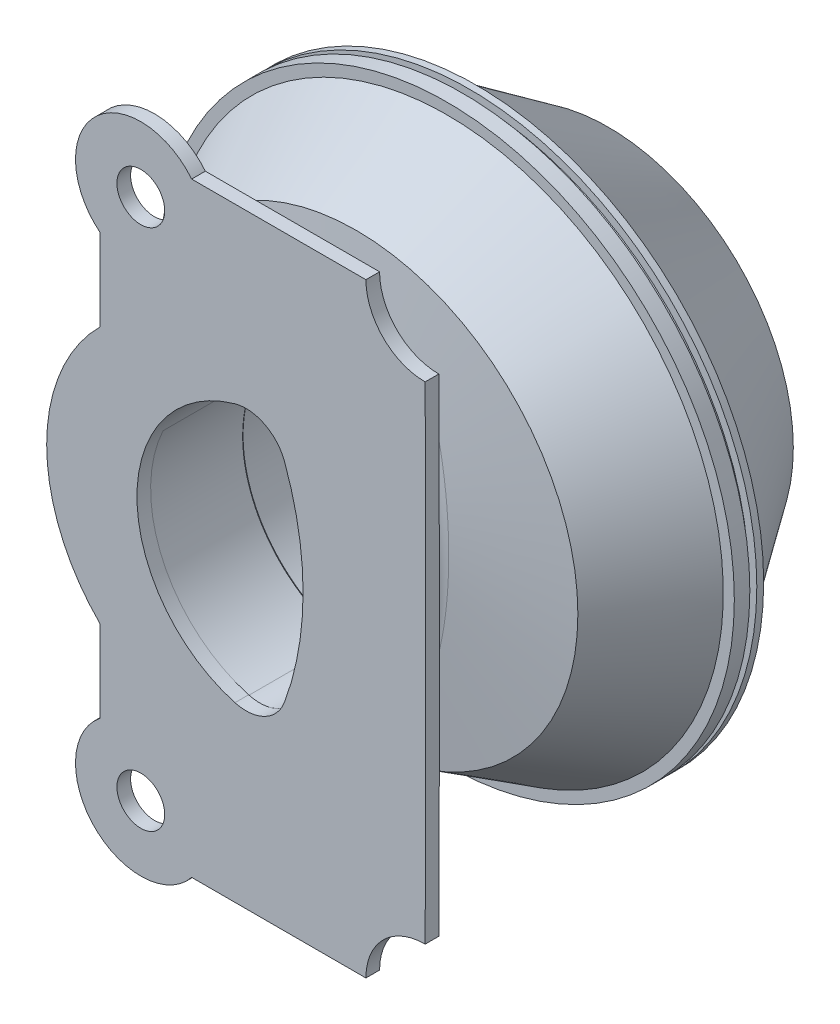
SolidWorks part; units mm, degrees
ref_plane "Front Plane" through (0, 0, 0) normal (0, 0, 1) x (1, 0, 0)
ref_plane "Top Plane" through (0, 0, 0) normal (0, 1, 0) x (1, 0, 0)
ref_plane "Right Plane" through (0, 0, 0) normal (1, 0, 0) x (0, 0, -1)
sketch "Sketch1" plane through (0, 0, 0) normal (0, 1, 0) x (1, 0, 0)
  line L0 (0, 0) -> (-41.1885, 4.2999)
  line L1 (-41.1885, 4.2999) -> (-51.3591, 21.1683)
  line L2 (-51.3591, 21.1683) -> (-53.4092, 21.1683)
  line L3 (-53.4092, 21.1683) -> (-53.4092, 24.0516)
  line L4 (-53.4092, 24.0516) -> (-51.9382, 24.0516)
  line L5 (-51.9382, 24.0516) -> (-51.9382, 25.3468)
  line L6 (-51.9382, 25.3468) -> (-53.4092, 25.3468)
  line L7 (-53.4092, 25.3468) -> (-53.4092, 26.625)
  line L8 (-53.4092, 26.625) -> (-51.4678, 26.625)
  line L9 (-51.4678, 26.625) -> (-34.3992, 51.1461)
  line L10 (-34.3992, 51.1461) -> (0, 57.3101)
  line L11 (0, 57.3101) -> (0, 0) construction
  line L12 (0, 0) -> (0, 57.3101)
  dimension "D1" = 57.4512
revolve "Revolve1" add sketch "Sketch1" angle 360 about L11
sketch "Sketch2" plane through (0, 0, 0) normal (0, 0, 1) x (1, 0, 0)
  arc A0 (-0.5749, 23.8806) -> (-0.5749, -24.2496) centre (6.2102, -0.1845) ccw
  arc A1 (8.6443, 19.1775) -> (8.6443, -19.5465) centre (-43.9843, -0.1845) cw
  arc A2 (8.6443, 19.1775) -> (-0.5749, 23.8806) centre (1.4929, 16.5465) ccw
  arc A3 (8.6443, -19.5465) -> (-0.5749, -24.2496) centre (1.4929, -16.9155) cw
  arc A4 (13.4119, 20.9315) -> (13.4119, -21.3005) centre (-43.9843, -0.1845) cw
  arc A5 (13.4119, -21.3005) -> (-1.9535, -29.139) centre (1.4929, -16.9155) cw
  arc A6 (-1.9535, 28.77) -> (-1.9535, -29.139) centre (6.2102, -0.1845) ccw
  arc A7 (13.4119, 20.9315) -> (-1.9535, 28.77) centre (1.4929, 16.5465) ccw
  dimension "D1" = 5.08
extrude "Extrude1" add sketch "Sketch2" along normal blind 15.24 and the other way up to next
fillet "Fillet1" radius 2.54 4 edges at (-23.8298, 1.4298, -2.4922) (6.4239, -28.6192, -3.0621) (17.1636, -1.2558, -1.7966) (6.4242, 28.2501, -3.0245)
ref_plane "Plane1" through (0, 0, 15.24) normal (0, 0, 1) x (1, 0, 0)
sketch "Sketch3" plane through (0, 0, 15.24) normal (0, 0, 1) x (1, 0, 0)
  line L0 (-25.6087, 23.8607) -> (-25.6087, 39.1449)
  line L1 (34.8116, -56.22) -> (-8.5336, -56.22)
  line L3 (34.8116, 56.22) -> (-8.5336, 56.22)
  line L4 (-25.6087, -39.1449) -> (-25.6087, -23.8607)
  arc A0 (34.8116, -56.22) -> (34.8116, 56.22) centre (-8901.9101, 0) ccw
  arc A1 (-25.6087, 23.8607) -> (-25.6087, -23.8607) centre (-1.748, 0) ccw
  arc A4 (-8.5336, 56.22) -> (-25.6087, 39.1449) centre (-17.9887, 48.6) ccw
  arc A5 (-25.6087, -39.1449) -> (-8.5336, -56.22) centre (-17.9887, -48.6) ccw
extrude "Extrude2" add sketch "Sketch3" along normal blind 2.54
sketch "Sketch4" plane through (173.7459, 16.0148, 17.78) normal (0, 0, 1) x (1, 0, 0)
  circle A0 centre (-191.7346, 32.5852) radius 4.445
  circle A1 centre (-191.7346, -64.6148) radius 4.445
  dimension "D1" = 8.89
extrude "Cut-Extrude1" cut sketch "Sketch4" against normal up to next
fillet "Fillet2" radius 2.54 4 edges at (17.173, -0.1845, 15.24) (7.2641, -28.2285, 15.24) (-23.8731, -0.1845, 15.24) (7.2641, 27.8595, 15.24)
sketch "Sketch5" plane through (0, 0, 17.78) normal (0, 0, 1) x (1, 0, 0)
  circle A0 centre (34.8116, 56.22) radius 10.9518
  circle A1 centre (34.8116, -56.22) radius 10.9518
extrude "Cut-Extrude2" cut sketch "Sketch5" against normal blind 2.54
sketch "Sketch6" plane through (25.8959, 34.9259, 17.78) normal (0, 0, 1) x (1, 0, 0)
  arc A0 (-26.3845, -10.8608) -> (-26.3845, -58.9909) centre (-19.5994, -34.9259) ccw
  arc A1 (-17.1653, -15.5638) -> (-17.1653, -54.2879) centre (-69.7939, -34.9259) cw
  arc A2 (-17.1653, -15.5638) -> (-26.3845, -10.8608) centre (-24.3167, -18.1948) ccw
  arc A3 (-17.1653, -54.2879) -> (-26.3845, -58.9909) centre (-24.3167, -51.6569) cw
extrude "Cut-Extrude3" cut sketch "Sketch6" against normal blind 30.48
